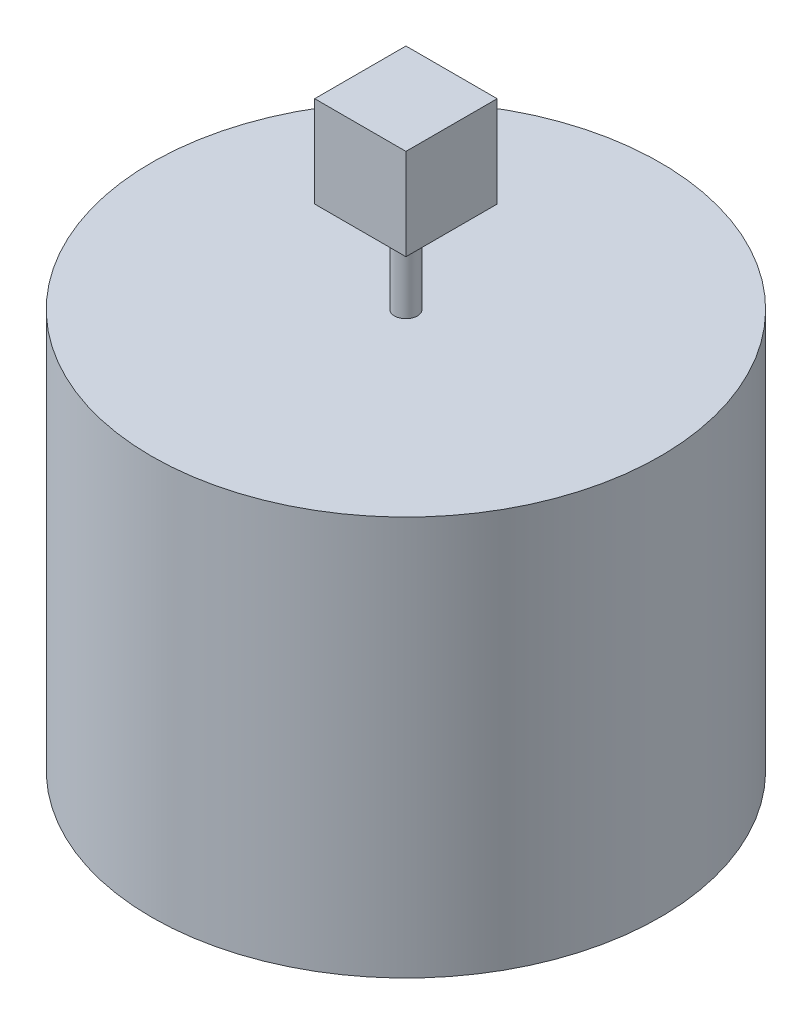
SolidWorks part; units mm, degrees
ref_plane "Plan de face" through (0, 0, 0) normal (0, 0, 1) x (1, 0, 0)
ref_plane "Plan de dessus" through (0, 0, 0) normal (0, 1, 0) x (1, 0, 0)
ref_plane "Plan de droite" through (0, 0, 0) normal (1, 0, 0) x (0, 0, -1)
sketch "Esquisse1" plane through (0, 0, 0) normal (0, 1, 0) x (1, 0, 0)
  circle A0 centre (0, 0) radius 223
  dimension "D1" = 446
extrude "Extrusion1" add sketch "Esquisse1" along normal blind 350
sketch "Esquisse2" plane through (0, 350, 0) normal (0, 1, 0) x (1, 0, 0)
  circle A0 centre (0, 0) radius 10
  dimension "D1" = 20
extrude "Extrusion2" add sketch "Esquisse2" along normal blind 80
sketch "Esquisse3" plane through (0, 430, 0) normal (0, 1, 0) x (1, 0, 0)
  line L0 (0, -10) -> (0, 40) construction
  line L1 (-10, 0) -> (40, 0) construction
  line L3 (-40, -40) -> (40, -40)
  line L4 (-40, -40) -> (-40, 40)
  line L5 (-40, 40) -> (40, 40)
  line L6 (40, -40) -> (40, 40)
  circle A0 centre (0, 0) radius 10 construction
  dimension "D1" = 80
extrude "Extrusion3" add sketch "Esquisse3" along normal blind 80
